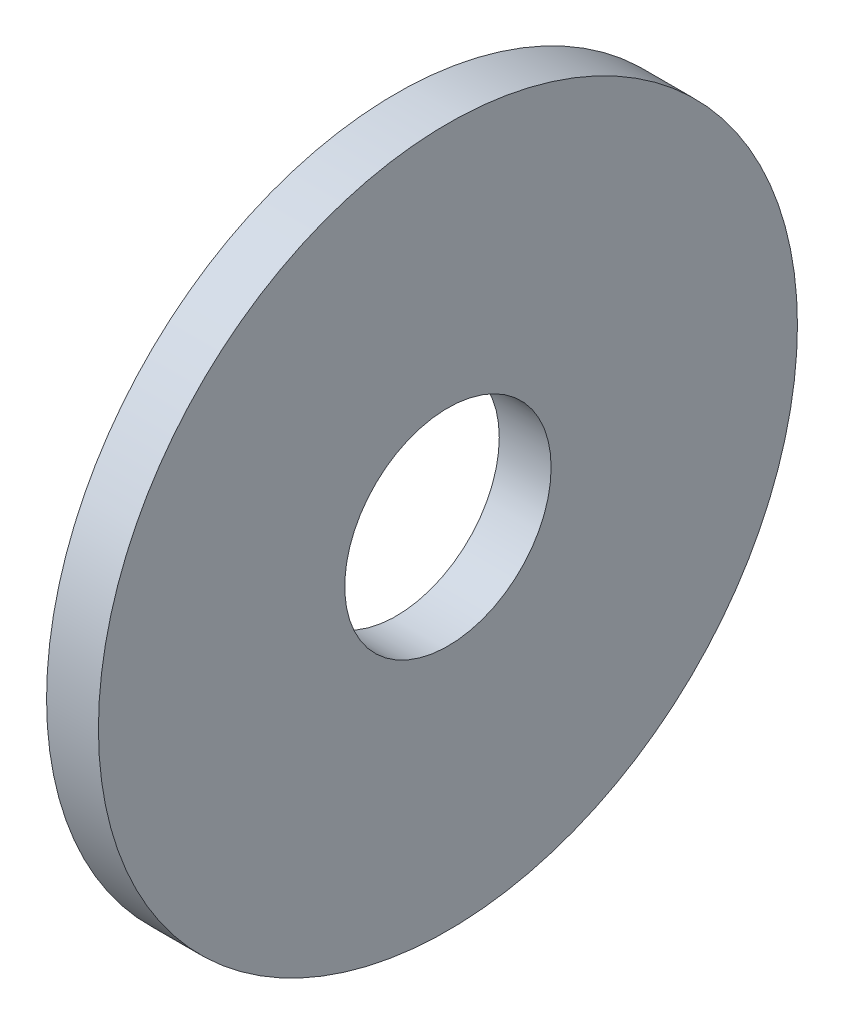
SolidWorks part; units mm, degrees
material "Plain Carbon Steel"
ref_plane "Front Plane" through (0, 0, 0) normal (0, 0, 1) x (1, 0, 0)
ref_plane "Top Plane" through (0, 0, 0) normal (0, 1, 0) x (1, 0, 0)
ref_plane "Right Plane" through (0, 0, 0) normal (1, 0, 0) x (0, 0, -1)
sketch "Sketch1" plane through (0, 0, 0) normal (1, 0, 0) x (0, 0, -1)
  circle A0 centre (0, 0) radius 8.7312
  circle A1 centre (0, 0) radius 2.5781
  dimension "OD" = 17.4625
  dimension "ID" = 5.1562
extrude "Boss-Extrude1" add sketch "Sketch1" along normal blind 1.2954
